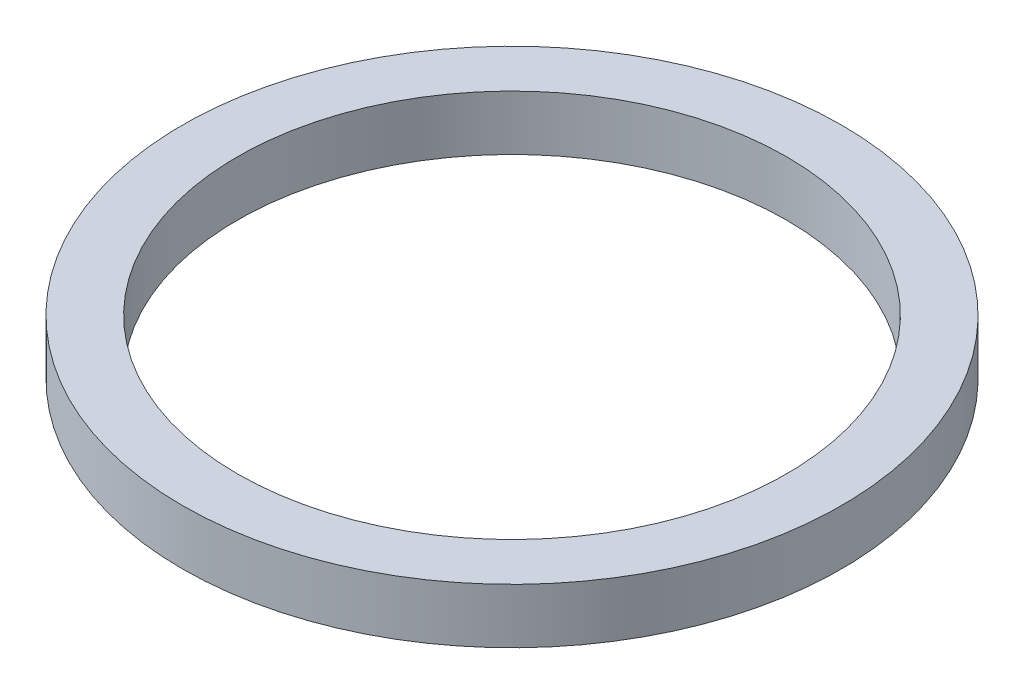
SolidWorks part; units mm, degrees
ref_plane "Front Plane" through (0, 0, 0) normal (0, 0, 1) x (1, 0, 0)
ref_plane "Top Plane" through (0, 0, 0) normal (0, 1, 0) x (1, 0, 0)
ref_plane "Right Plane" through (0, 0, 0) normal (1, 0, 0) x (0, 0, -1)
sketch "Sketch1" plane through (0, 0, 0) normal (0, 1, 0) x (1, 0, 0)
  circle A0 centre (0, 0) radius 25
  circle A1 centre (0, 0) radius 30
  dimension "D1" = 50
  dimension "D2" = 5
extrude "Boss-Extrude1" add sketch "Sketch1" along normal blind 5
